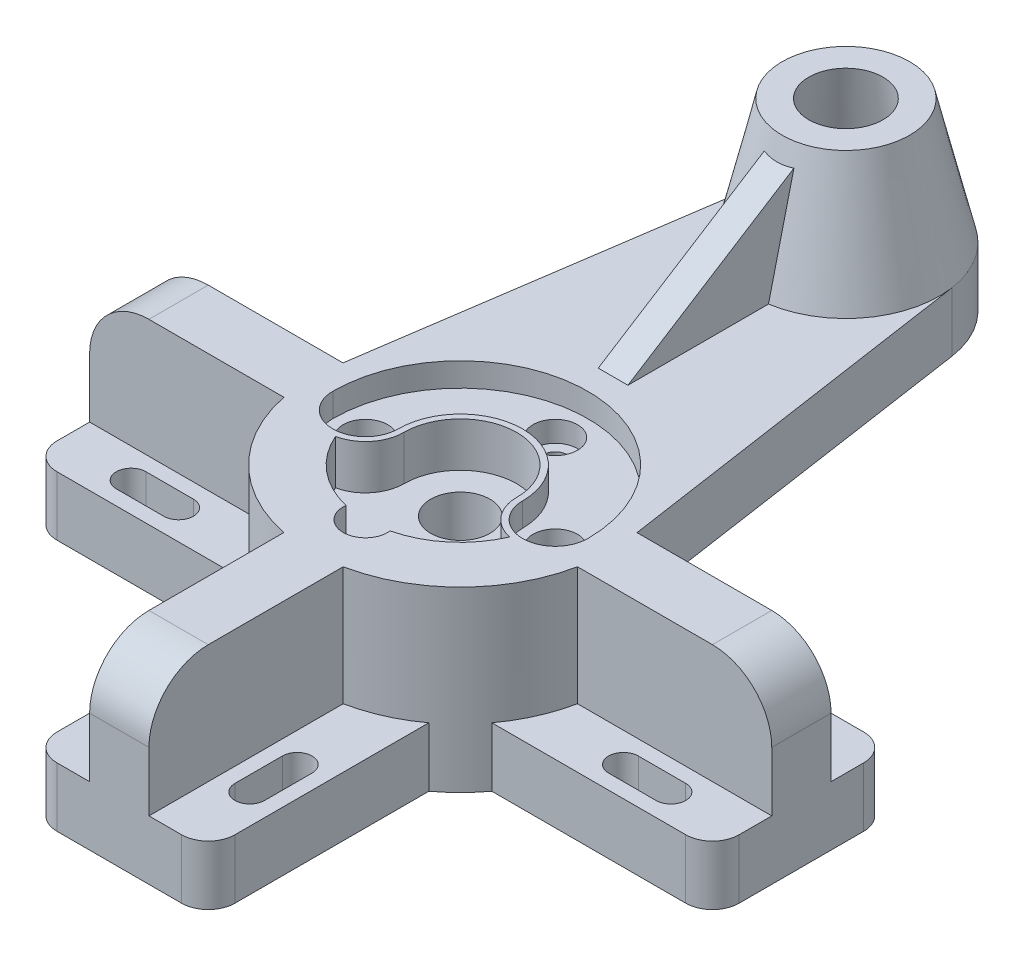
SolidWorks part; units mm, degrees
material "1060 Alloy"
ref_plane "Front Plane" through (0, 0, 0) normal (0, 0, 1) x (1, 0, 0)
ref_plane "Top Plane" through (0, 0, 0) normal (0, 1, 0) x (1, 0, 0)
ref_plane "Right Plane" through (0, 0, 0) normal (1, 0, 0) x (0, 0, -1)
sketch "Sketch1" plane through (0, 0, 0) normal (0, 1, 0) x (1, 0, 0)
  circle A2 centre (0, 0) radius 50.5
  dimension "D1" = 101
extrude "Boss-Extrude1" add sketch "Sketch1" along normal blind 60
sketch "Sketch2" plane through (0, 0, 0) normal (0, -1, 0) x (1, 0, 0)
  line L0 (-30, 0) -> (-30, 115)
  line L1 (30, 115) -> (30, 0)
  line L2 (30, 0) -> (-30, 0)
  line L3 (-30, 115) -> (30, 115)
  point P2 (0, 0)
  dimension "D1" = 60
  dimension "D2" = 115
extrude "Boss-Extrude2" add sketch "Sketch2" against normal blind 20
sketch "Sketch3" plane through (0, 0, 0) normal (0, 0, 1) x (1, 0, 0)
  line L0 (0, -13.9787) -> (0, 86.0542) construction
pattern_circular "CirPattern1" count 4 over 360 about axis through (0, 0, 0) along (0, 1, 0) skipping 2 of "Boss-Extrude2"
sketch "Sketch4" plane through (0, 60, 0) normal (0, 1, 0) x (1, 0, 0)
  line L0 (-49.9577, 7.3808) -> (-31.1617, 134.6038)
  line L1 (31.1617, 134.6038) -> (49.9577, 7.3808)
  line L2 (30, -115) -> (-30, -115) construction
  arc A1 (49.9577, 7.3808) -> (-49.9577, 7.3808) centre (0, 0) cw
  arc A4 (-31.1617, 134.6038) -> (31.1617, 134.6038) centre (0, 130) cw
  circle A6 centre (0, 0) radius 50.5 construction
  dimension "D2" = 31.5
  dimension "D1" = 245
extrude "Boss-Extrude3" add sketch "Sketch4" against normal blind 20
sketch "Sketch6" plane through (0, 20, 0) normal (0, 1, 0) x (1, 0, 0)
  line L0 (0, 0) -> (0, -151.4209) construction
  line L3 (20, -75) -> (20, -91) construction
  line L4 (25, -75) -> (25, -91)
  line L5 (15, -75) -> (15, -91)
  line L6 (30, -115) -> (-30, -115) construction
  line L7 (-20, -75) -> (-20, -91) construction
  line L8 (-25, -75) -> (-25, -91)
  line L9 (-15, -75) -> (-15, -91)
  arc A2 (25, -75) -> (15, -75) centre (20, -75) ccw
  arc A3 (15, -91) -> (25, -91) centre (20, -91) ccw
  arc A4 (-25, -75) -> (-15, -75) centre (-20, -75) cw
  arc A5 (-15, -91) -> (-25, -91) centre (-20, -91) cw
  point P5 (-20, -83)
  point P7 (20, -83)
  dimension "D1" = 5
  dimension "D2" = 16
  dimension "D3" = 24
  dimension "D4" = 20
fillet "Fillet1" radius 9 6 edges at (-115, 10, -30) (-115, 10, 30) (115, 10, -30) (115, 10, 30) (-30, 10, 115) (30, 10, 115)
sketch "Sketch8" plane through (0, 0, 0) normal (0, 0, 1) x (1, 0, 0)
  line L0 (-115, 20) -> (-115, 40)
  line L1 (-95, 60) -> (-45, 60)
  line L2 (-40.6233, 0) -> (-106, 0) construction
  line L3 (-45, 60) -> (-45, 20)
  line L4 (-40.6233, 20) -> (-106, 20) construction
  line L5 (-45, 20) -> (-115, 20)
  arc A0 (-115, 40) -> (-95, 60) centre (-95, 40) cw
  dimension "D1" = 60
  dimension "D2" = 20
  dimension "D3" = 50
extrude "Boss-Extrude4" add sketch "Sketch8" along normal mid plane 20
pattern_circular "CirPattern4" count 2 over 360 about axis through (0, -13.9787, 0) along (0, 1, 0) of "Boss-Extrude4"
sketch "Sketch9" plane through (0, 20, 0) normal (0, 1, 0) x (1, 0, 0)
  line L0 (0, 0) -> (0, -151.4209) construction
  line L1 (10, -115) -> (-10, -115)
  line L2 (10, -115) -> (10, -35)
  line L3 (10, -35) -> (-10, -35)
  line L4 (-10, -115) -> (-10, -35)
  line L5 (10, -115) -> (-10, -35) construction
  line L6 (10, -35) -> (-10, -115) construction
  line L7 (21, -115) -> (-21, -115) construction
  point P0 (0, -75)
  dimension "D1" = 20
  dimension "D2" = 80
extrude "Boss-Extrude5" add sketch "Sketch9" along normal up to surface (40 mm away) up to face at (0, 60, -25.5604)
fillet "Fillet2" radius 20 1 edges at (0, 60, 115)
ref_plane "Plane1" through (0, 102, 0) normal (0, 1, 0) x (1, 0, 0)
sketch "Sketch19" plane through (0, 60, 0) normal (0, 1, 0) x (1, 0, 0)
  arc A0 (-43, 0) -> (-21, 0) centre (-32, 0) ccw
  arc A1 (-21, 0) -> (21, 0) centre (0, 0) cw
  arc A2 (21, 0) -> (43, 0) centre (32, 0) ccw
  arc A3 (43, 0) -> (-43, 0) centre (0, 0) ccw
  dimension "D1" = 22
  dimension "D2" = 43
extrude "Cut-Extrude1" cut sketch "Sketch19" against normal blind 8
sketch "Sketch20" plane through (0, 60, 0) normal (0, 1, 0) x (1, 0, 0)
  line L0 (0, 0) -> (0, -151.4209) construction
  arc A0 (-19, 0) -> (19, 0) centre (0, 0) cw
  arc A1 (19, 0) -> (29.3594, -12.729) centre (32, 0) ccw
  arc A2 (29.3594, -12.729) -> (-29.3594, -12.729) centre (0, 0) cw
  arc A3 (-19, 0) -> (-29.3594, -12.729) centre (-32, 0) cw
  arc A4 (10, -49.5) -> (30, -40.6233) centre (0, 0) ccw construction
  arc A6 (-43, 0) -> (-21, 0) centre (-32, 0) ccw construction
  arc A7 (21, 0) -> (43, 0) centre (32, 0) ccw construction
  arc A8 (21, 0) -> (-21, 0) centre (0, 0) ccw construction
  dimension "D1" = 2
  dimension "D2" = 32
extrude "Cut-Extrude2" cut sketch "Sketch6" against normal through all both and the other way through all
extrude "Cut-Extrude3" cut sketch "Sketch20" against normal blind 15
pattern_circular "CirPattern5" count 4 over 360 about axis through (0, 0, 0) along (0, 1, 0) skipping 2 of "Cut-Extrude2"
sketch "Sketch21" plane through (0, 60, 0) normal (0, 1, 0) x (1, 0, 0)
  circle A0 centre (0, -32) radius 7.5
  arc A1 (-29.3594, -12.729) -> (29.3594, -12.729) centre (0, 0) ccw construction
  dimension "D1" = 15
extrude "Cut-Extrude4" cut sketch "Sketch21" against normal through all both and the other way through all
sketch "Sketch22" plane through (0, 45, 0) normal (0, 1, 0) x (1, 0, 0)
  circle A0 centre (0, 0) radius 10
  dimension "D1" = 20
extrude "Cut-Extrude5" cut sketch "Sketch22" against normal through all both
hole_wizard "CBORE for M12 Hex Head Cap Screw1" positions "Sketch23" profile "Sketch24" counterbore size "M12" standard "ANSI Metric" end condition through all
sketch "Sketch23" plane through (0, 52, 0) normal (0, 1, 0) x (1, 0, 0)
  line L0 (0, 43) -> (0, 21) construction
  arc A0 (-43, 0) -> (-21, 0) centre (-32, 0) ccw construction
  arc A3 (43, 0) -> (-43, 0) centre (0, 0) ccw construction
  arc A4 (21, 0) -> (-21, 0) centre (0, 0) ccw construction
  point P0 (-32, 0)
  point P2 (32, 0)
  point P12 (0, 32)
sketch "Sketch24" plane through (-32, 52, 0) normal (1, 0, 0) x (0, 0, 1)
  line L0 (0, 0) -> (0, 52)
  line L1 (0, 52) -> (4, 52)
  line L3 (4, 52) -> (4, 7)
  line L4 (4, 7) -> (7.5, 7)
  line L5 (7.5, 7) -> (7.5, 0)
  line L7 (7.5, 0) -> (0, 0)
  line L11 (0, -6.35) -> (0, 107.95) construction
  dimension "Thru Hole Dia." = 8
  dimension "Thru Hole Depth" = 52
  dimension "C'Bore Dia." = 15
  dimension "C'Bore Depth" = 7
sketch "Sketch25" plane through (0, 102, 0) normal (0, 1, 0) x (1, 0, 0)
  line L0 (0, -219.3846) -> (0, 304.9664) construction
sketch "Sketch26" plane through (0, 0, 0) normal (1, 0, 0) x (0, 0, -1)
  line L0 (161.5, 60) -> (151.5, 102)
  line L1 (151.5, 102) -> (130, 102)
  line L4 (130, 60) -> (161.5, 60)
  line L5 (130, -4.4165) -> (130, 118.2967) construction
  line L6 (130, 60) -> (130, 102)
  dimension "D1" = 42
  dimension "D2" = 63
  dimension "D3" = 43
revolve "Revolve1" add sketch "Sketch26" angle 360 about L5
sketch "Sketch17" plane through (0, 0, 0) normal (1, 0, 0) x (0, 0, -1)
  line L0 (106.8333, 95) -> (51.5, 60)
  line L1 (10, 60) -> (134.6038, 60) construction
  line L2 (10, 40) -> (134.6038, 40) construction
  line L3 (161.5, 40) -> (161.5, 60) construction
  line L4 (108.5, 102) -> (98.5, 60) construction
  dimension "D1" = 55
  dimension "D2" = 110
rib "Rib1" sketch "Sketch17" sketch "Sketch17" thickness 10 extrusion direction parallel to sketch draft on no parameters "D1"=10
sketch "Sketch29" plane through (0, 102, 0) normal (0, 1, 0) x (1, 0, 0)
  line L0 (0, -219.3846) -> (0, 304.9664) construction
  circle A0 centre (0, 130) radius 21.5 construction
  point P0 (0, 151.5)
sketch "Sketch27" plane through (0, 0, 0) normal (1, 0, 0) x (0, 0, -1)
  line L0 (142.5, 102) -> (152.5, 40)
  line L1 (-219.3846, 102) -> (304.9664, 102) construction
  line L2 (134.6038, 40) -> (161.5, 40) construction
  line L3 (152.5, 40) -> (130, 40)
  line L4 (130, 40) -> (130, 102)
  line L5 (130, 102) -> (142.5, 102)
  line L6 (130, 116.7192) -> (130, 15.039) construction
  dimension "D1" = 25
  dimension "D2" = 45
  dimension "D3" = 21.5
revolve "Cut-Revolve1" cut sketch "Sketch27" angle 360 about L6
equation "\"A\"= 245"
equation "\"B\"= 63"
equation "\"C\"= 110"
equation "\"D\"= 42"
equation "\"X\"= \"D\" / 2 + 3"
equation "\"Y\"= \"C\" / 2 + 5"
equation "\"D1@Boss-Extrude1\"=\"Y\""
equation "\"D1@Sketch4\"=\"A\""
equation "\"D3@Sketch6\"=\"X\""
equation "\"D1@Sketch8\"=\"Y\""
equation "\"D2@Sketch17\"=\"C\""
equation "\"D1@Sketch26\"=\"D\""
equation "\"D2@Sketch26\"=\"B\""
equation "\"D2@Sketch4\"=\"B\"/2"
